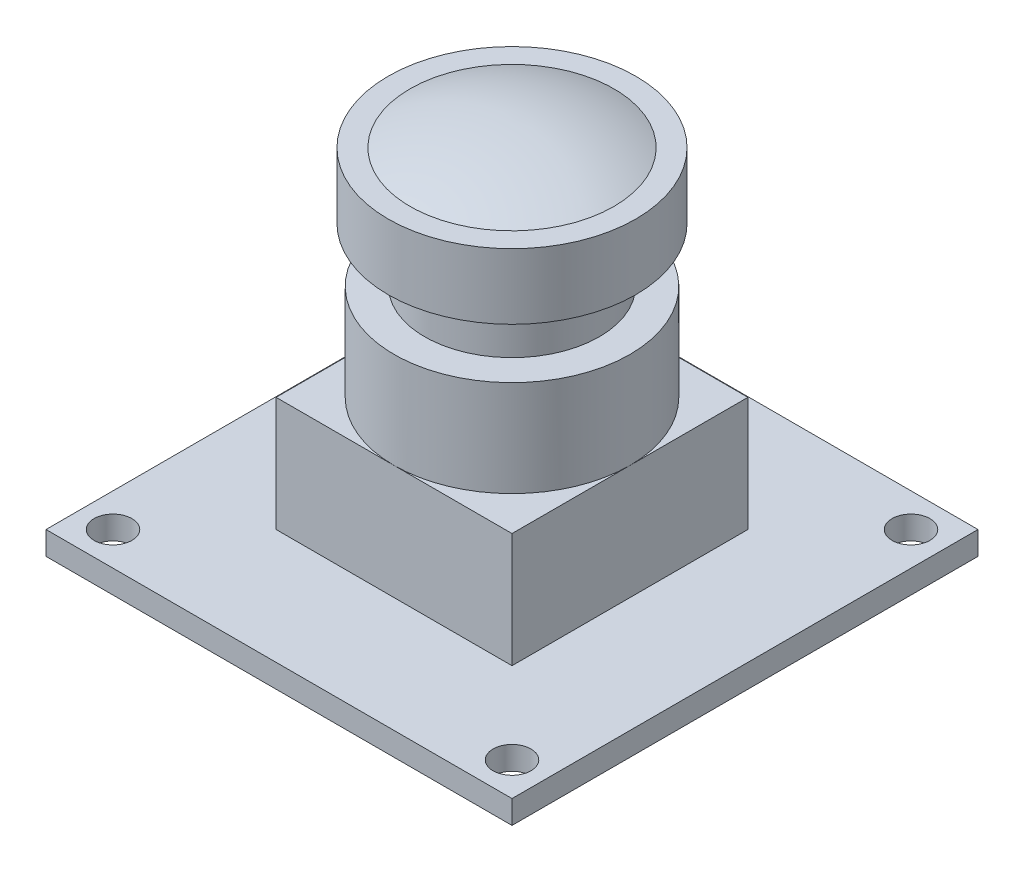
SolidWorks part; units mm, degrees
ref_plane "Front Plane" through (0, 0, 0) normal (0, 0, 1) x (1, 0, 0)
ref_plane "Top Plane" through (0, 0, 0) normal (0, 1, 0) x (1, 0, 0)
ref_plane "Right Plane" through (0, 0, 0) normal (1, 0, 0) x (0, 0, -1)
sketch "Sketch1" plane through (0, 0, 0) normal (0, 1, 0) x (1, 0, 0)
  line L1 (-16, -16) -> (16, -16)
  line L2 (-16, -16) -> (-16, 16)
  line L3 (-16, 16) -> (16, 16)
  line L4 (16, -16) -> (16, 16)
  line L5 (-16, -16) -> (16, 16) construction
  line L6 (-16, 16) -> (16, -16) construction
  circle A0 centre (-13.7, 13.7) radius 1.3
  circle A1 centre (13.7, 13.7) radius 1.3
  circle A2 centre (13.7, -13.7) radius 1.3
  circle A3 centre (-13.7, -13.7) radius 1.3
  point P0 (0, 0)
  dimension "D2" = 2.6
  dimension "D3" = 2.3
  dimension "D1" = 32
extrude "Boss-Extrude1" add sketch "Sketch1" along normal blind 1.6
sketch "Sketch2" plane through (0, 1.6, 0) normal (0, 1, 0) x (1, 0, 0)
  line L1 (-8.1, -8.1) -> (8.1, -8.1)
  line L2 (-8.1, -8.1) -> (-8.1, 8.1)
  line L3 (-8.1, 8.1) -> (8.1, 8.1)
  line L4 (8.1, -8.1) -> (8.1, 8.1)
  line L5 (-8.1, -8.1) -> (8.1, 8.1) construction
  line L6 (-8.1, 8.1) -> (8.1, -8.1) construction
  point P0 (0, 0)
  dimension "D1" = 16.2
extrude "Boss-Extrude2" add sketch "Sketch2" along normal blind 7.86
sketch "Sketch4" plane through (0, 0, 0) normal (0, 0, 1) x (1, 0, 0)
  line L0 (0, 9.46) -> (0, 24.31)
  line L1 (8.1, 9.46) -> (-8.1, 9.46) construction
  line L2 (0, 24.31) -> (8.5, 24.31)
  line L3 (8.5, 24.31) -> (8.5, 19.81)
  line L4 (8.5, 19.81) -> (6, 19.81)
  line L5 (6, 19.81) -> (6, 16.06)
  line L6 (6, 16.06) -> (8.1, 16.06)
  line L7 (8.1, 16.06) -> (8.1, 9.46)
  line L8 (0, 24.31) -> (0, 25.81)
  line L9 (0, 25.81) -> (-7.8315, 25.81) construction
  line L10 (0, 9.46) -> (8.1, 9.46)
  arc A0 (0, 25.81) -> (7, 24.31) centre (0, 8.7267) cw
  dimension "D1" = 6
  dimension "D2" = 4.5
  dimension "D3" = 8.5
  dimension "D4" = 6.6
  dimension "D5" = 3.75
  dimension "D6" = 7
  dimension "D7" = 1.5
revolve "Revolve3" add sketch "Sketch4" angle 360 about L0
